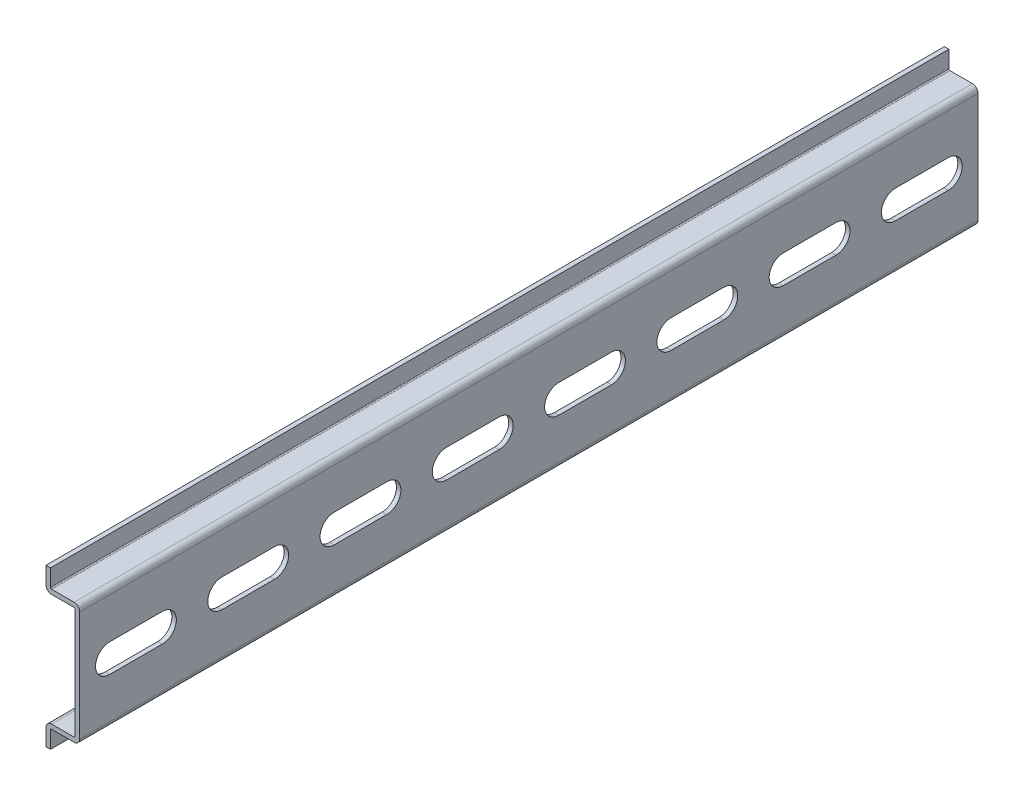
SolidWorks part; units mm, degrees
ref_plane "Front Plane" through (0, 0, 0) normal (0, 0, 1) x (1, 0, 0)
ref_plane "Top Plane" through (0, 0, 0) normal (0, 1, 0) x (1, 0, 0)
ref_plane "Right Plane" through (0, 0, 0) normal (1, 0, 0) x (0, 0, -1)
sketch "Sketch1" plane through (0, 0, 0) normal (0, 0, 1) x (1, 0, 0)
  line L0 (0, -13.5) -> (0, 13.5) construction
  line L1 (0, 13.5) -> (-6.5, 13.5) construction
  line L2 (-6.5, 13.5) -> (-6.5, 17.5) construction
  line L3 (0, -13.5) -> (-6.5, -13.5) construction
  line L4 (-6.5, -13.5) -> (-6.5, -17.5) construction
  line L5 (-7.5, 0) -> (0, 0) construction
  line L6 (-6.5, 17.5) -> (-7.5, 17.5) construction
  line L7 (-7.5, 0) -> (-7.5, 17.5) construction
  dimension "D1" = 27
  dimension "Height" = 35
  dimension "Depth" = 7.5
  dimension "Metal Thickness" = 1
sketch "Sketch2" plane through (0, 0, 0) normal (1, 0, 0) x (0, 0, -1)
  line L0 (0, 0) -> (-200.025, 0) construction
  line L1 (-62.5, 17.5) -> (-62.5, -17.5) construction
  line L2 (-137.525, 17.5) -> (-137.525, -17.5) construction
  line L3 (-62.5, 17.5) -> (-137.525, 17.5) construction
  line L4 (-100.0125, 0) -> (-100.0125, 17.5) construction
  point P8 (-137.525, 0)
  point P9 (-62.5, 0)
  point P14 (-100.0125, 17.5)
  dimension "Length" = 200.025
  dimension "D1" = 62.5
sketch "Sketch3" plane through (0, 0, 0) normal (0, 0, 1) x (1, 0, 0)
  line L0 (-6.5, -13.5) -> (-6.5, -17.5) construction
  line L1 (0, -13.5) -> (-6.5, -13.5) construction
  line L2 (0, -13.5) -> (0, 13.5) construction
  line L3 (0, 13.5) -> (-6.5, 13.5) construction
  line L4 (-6.5, 13.5) -> (-6.5, 17.5) construction
  line L5 (-6.5, -13.5) -> (-6.5, -17.5)
  line L6 (0, -13.5) -> (-6.5, -13.5)
  line L7 (0, -13.5) -> (0, 13.5)
  line L8 (0, 13.5) -> (-6.5, 13.5)
  line L9 (-6.5, 13.5) -> (-6.5, 17.5)
extrude "Extrude-Thin1" add sketch "Sketch3" along normal up to vertex (200.025 mm away) thin
sketch "Sketch4" plane through (0, 0, 0) normal (1, 0, 0) x (0, 0, -1)
  line L0 (0, 0) -> (-62.1077, 0) construction
  line L1 (-6.65, 0) -> (-18.35, 0) construction
  line L2 (-6.65, -3.15) -> (-18.35, -3.15)
  line L3 (-6.65, 3.15) -> (-18.35, 3.15)
  arc A0 (-6.65, -3.15) -> (-6.65, 3.15) centre (-6.65, 0) ccw
  arc A1 (-18.35, 3.15) -> (-18.35, -3.15) centre (-18.35, 0) ccw
  point P5 (-12.5, 0)
  point P10 (-3.5, 0)
  point P11 (-21.5, 0)
  point P12 (-37.5, 0)
  dimension "D1" = 18
  dimension "Mounting Hole Diameter" = 6.3
  dimension "D3" = 12.5
  dimension "Mounting Hole C to C" = 25
extrude "Cut-Extrude1" cut sketch "Sketch4" against normal through all both and the other way through all
pattern_linear "LPattern1" count 32 spacing 25 along (0, 0, 1) of "Cut-Extrude1"
fillet "Fillet1" radius 0.25 4 edges at (-6.5, 13.5, 100.0125) (-6.5, -13.5, 100.0125) (-1, 12.5, 100.0125) (-1, -12.5, 100.0125)
fillet "Fillet2" radius 1.25 4 edges at (-7.5, -12.5, 100.0125) (0, -13.5, 100.0125) (0, 13.5, 100.0125) (-7.5, 12.5, 100.0125)
ref_plane "Contact Plane 1" through (-1, 0, 0) normal (-1, 0, 0) x (0, 0, 1)
equation "\"D3@LPattern1\" = \"Mounting Hole C to C@Sketch4\""
equation "\"D5@Extrude-Thin1\"=\"Metal Thickness@Sketch1\""
equation "\"D3@Sketch4\"=\"Mounting Hole C to C@Sketch4\"/2"
equation "\"D1@LPattern1\"=\"Length@Sketch2\"/\"Mounting Hole Diameter@Sketch4\""
